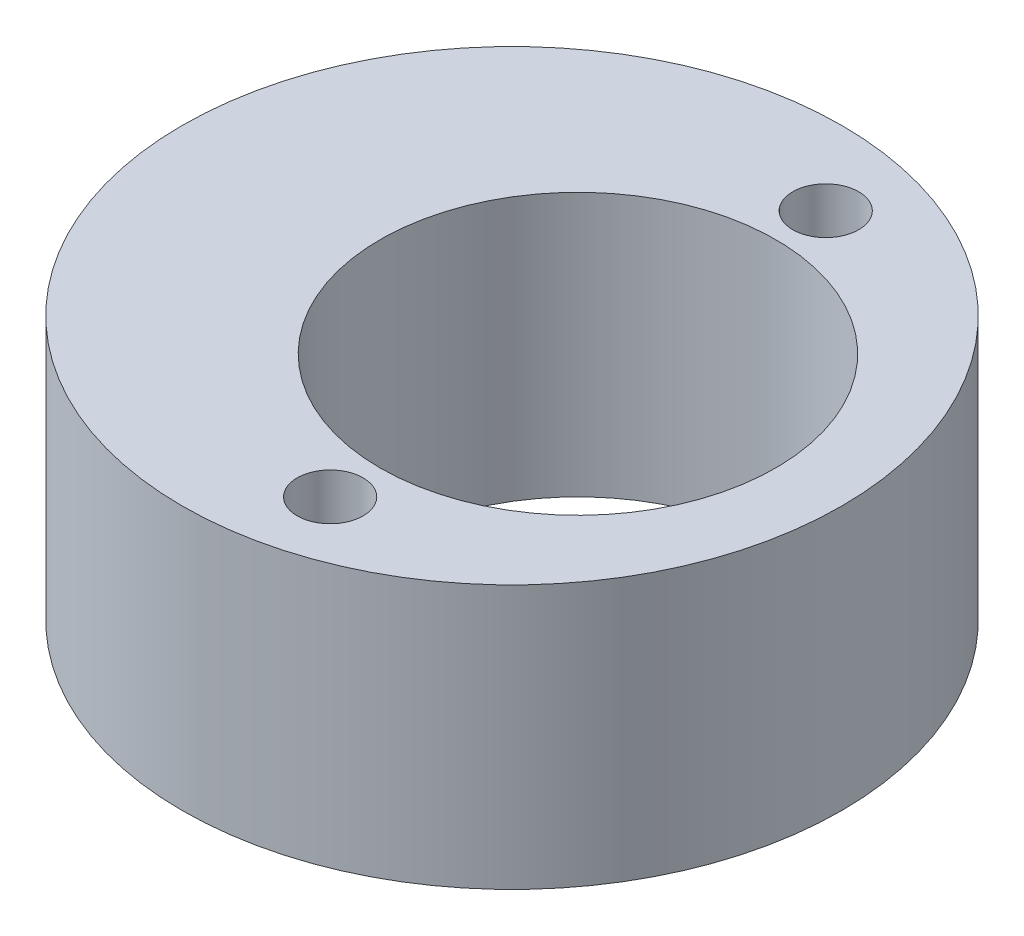
SolidWorks part; units mm, degrees
ref_plane "Front Plane" through (0, 0, 0) normal (0, 0, 1) x (1, 0, 0)
ref_plane "Top Plane" through (0, 0, 0) normal (0, 1, 0) x (1, 0, 0)
ref_plane "Right Plane" through (0, 0, 0) normal (1, 0, 0) x (0, 0, -1)
sketch "Sketch1" plane through (0, 0, 0) normal (0, 1, 0) x (1, 0, 0)
  line L0 (-1, 0) -> (0, 0) construction
  circle A0 centre (0, 0) radius 3
  circle A1 centre (-1, 0) radius 5
  dimension "D1" = 6
  dimension "D2" = 10
  dimension "D3" = 1
extrude "Boss-Extrude1" add sketch "Sketch1" along normal blind 4
sketch "Sketch2" plane through (0, 4, 0) normal (0, 1, 0) x (1, 0, 0)
  line L0 (0, 3.7579) -> (0, -3.7579) construction
  circle A0 centre (0, 3.7579) radius 0.5
  circle A1 centre (0, -3.7579) radius 0.5
  point P4 (0, 0)
  dimension "D1" = 1
  dimension "D2" = 1
  dimension "D3" = 0
extrude "Cut-Extrude1" cut sketch "Sketch2" against normal through all
